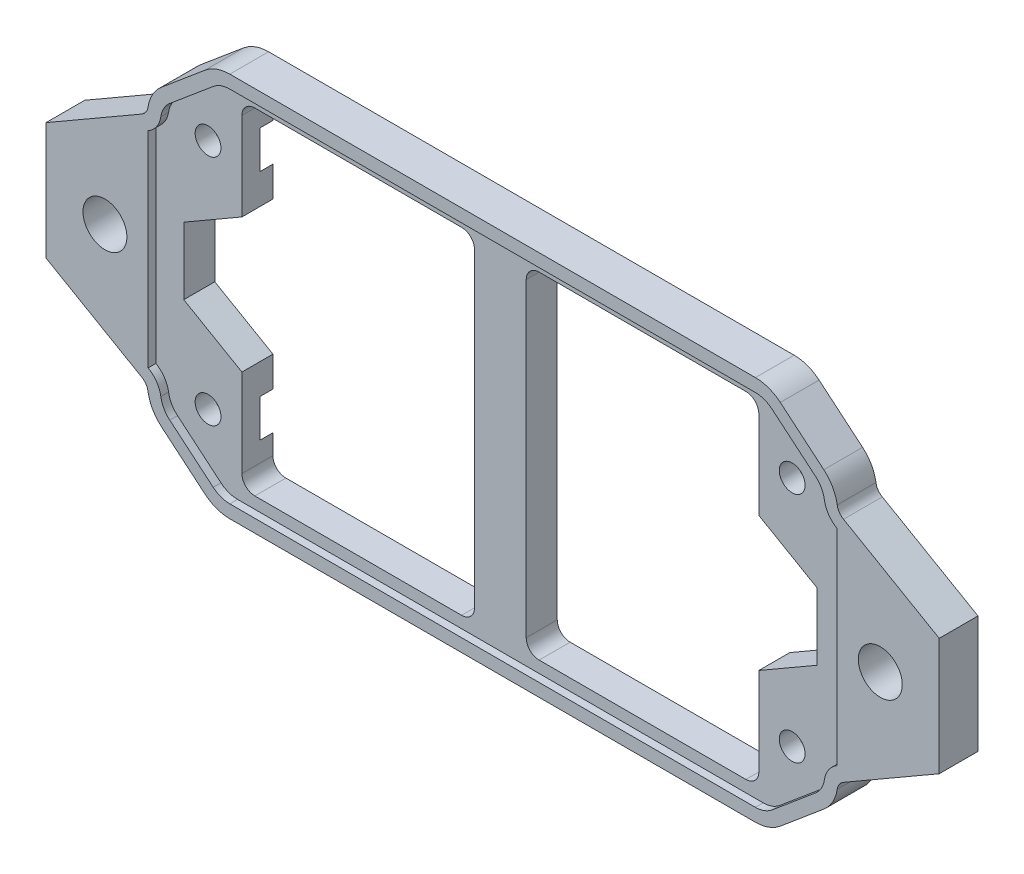
SolidWorks part; units mm, degrees
ref_plane "前视基准面" through (0, 0, 0) normal (0, 0, 1) x (1, 0, 0)
ref_plane "上视基准面" through (0, 0, 0) normal (0, 1, 0) x (1, 0, 0)
ref_plane "右视基准面" through (0, 0, 0) normal (1, 0, 0) x (0, 0, -1)
sketch "草图1" plane through (0, 0, 0) normal (0, 0, 1) x (1, 0, 0)
  line L0 (-6.82, 22.2889) -> (-10.184, 25.1116) construction
  line L1 (-6.4628, 3.3683) -> (-6.4628, 21.5229) construction
  line L2 (-10.184, -0.2205) -> (-6.82, 2.6022) construction
  line L3 (-51.4988, -0.4544) -> (-10.8267, -0.4544) construction
  line L4 (-55.5056, 2.6022) -> (-52.1416, -0.2205) construction
  line L5 (-55.8628, 21.5229) -> (-55.8628, 3.3683) construction
  line L6 (-10.8267, 25.3456) -> (-51.4988, 25.3456) construction
  line L7 (-52.1416, 25.1116) -> (-55.5056, 22.2889) construction
  line L8 (-53.7823, 21.4456) -> (-53.7823, 3.4456) construction
  line L9 (-53.7823, 3.4456) -> (-8.5823, 3.4456) construction
  line L10 (-8.5823, 3.4456) -> (-8.5823, 21.4456) construction
  line L11 (-8.5823, 21.4456) -> (-53.7823, 21.4456) construction
  line L12 (-52.7844, 25.8777) -> (-56.1484, 23.0549)
  line L13 (-56.8628, 21.5229) -> (-56.8628, 3.3683)
  line L14 (-56.1484, 1.8362) -> (-52.7844, -0.9865)
  line L15 (-51.4988, -1.4544) -> (-10.8267, -1.4544)
  line L16 (-9.5412, -0.9865) -> (-6.1772, 1.8362)
  line L17 (-5.4628, 3.3683) -> (-5.4628, 21.5229)
  line L18 (-6.1772, 23.0549) -> (-9.5412, 25.8777)
  line L19 (-10.8267, 26.3456) -> (-51.4988, 26.3456)
  line L20 (-53.4272, 26.6437) -> (-56.7911, 23.821)
  line L28 (-56.7911, 1.0701) -> (-53.4272, -1.7526)
  line L29 (-51.4988, -2.4544) -> (-10.8267, -2.4544)
  line L30 (-8.8984, -1.7526) -> (-5.5344, 1.0701)
  line L32 (-5.5344, 23.821) -> (-8.8984, 26.6437)
  line L33 (-10.8267, 27.3456) -> (-51.4988, 27.3456)
  line L34 (-57.8628, 12.4456) -> (-4.4628, 12.4456) construction
  line L35 (-57.8628, 21.5229) -> (-57.8628, 3.3683) construction
  line L36 (-58.3169, 21.2606) -> (-65.7239, 16.9842)
  line L37 (-65.7239, 16.9842) -> (-65.7239, 7.9069)
  line L38 (-65.7239, 7.9069) -> (-58.3169, 3.6305)
  line L42 (-50.0016, 7.9069) -> (-50.0016, 12.4456) [skipped]
  line L43 (-57.8628, 3.3683) -> (-56.8628, 3.9456) [skipped]
  line L44 (-53.7823, 19.167) -> (-53.9322, 19.2535) [skipped]
  line L45 (-31.1628, 27.3456) -> (-31.1628, -2.4544) construction
  line L46 (3.3984, 7.9069) -> (-4.0086, 3.6305)
  line L47 (3.3984, 16.9842) -> (3.3984, 7.9069)
  line L48 (-4.0086, 21.2606) -> (3.3984, 16.9842)
  line L49 (-4.4628, 3.3683) -> (-4.4628, 21.5229) construction
  arc A0 (-53.7823, 4.4456) -> (-53.7823, 2.4456) centre (-53.7823, 3.4456) ccw
  arc A1 (-53.7823, 2.4456) -> (-53.7823, 4.4456) centre (-53.7823, 3.4456) ccw
  arc A2 (-53.7823, 22.4456) -> (-53.7823, 20.4456) centre (-53.7823, 21.4456) ccw
  arc A3 (-53.7823, 20.4456) -> (-53.7823, 22.4456) centre (-53.7823, 21.4456) ccw
  arc A4 (-8.5823, 4.4456) -> (-8.5823, 2.4456) centre (-8.5823, 3.4456) ccw
  arc A5 (-8.5823, 2.4456) -> (-8.5823, 4.4456) centre (-8.5823, 3.4456) ccw
  arc A6 (-8.5823, 22.4456) -> (-8.5823, 20.4456) centre (-8.5823, 21.4456) ccw
  arc A7 (-8.5823, 20.4456) -> (-8.5823, 22.4456) centre (-8.5823, 21.4456) ccw
  arc A8 (-10.184, 25.1116) -> (-10.8267, 25.3456) centre (-10.8267, 24.3456) ccw construction
  arc A9 (-6.4628, 21.5229) -> (-6.82, 22.2889) centre (-7.4628, 21.5229) ccw construction
  arc A10 (-6.82, 2.6022) -> (-6.4628, 3.3683) centre (-7.4628, 3.3683) ccw construction
  arc A11 (-10.8267, -0.4544) -> (-10.184, -0.2205) centre (-10.8267, 0.5456) ccw construction
  arc A12 (-52.1416, -0.2205) -> (-51.4988, -0.4544) centre (-51.4988, 0.5456) ccw construction
  arc A13 (-55.8628, 3.3683) -> (-55.5056, 2.6022) centre (-54.8628, 3.3683) ccw construction
  arc A14 (-55.5056, 22.2889) -> (-55.8628, 21.5229) centre (-54.8628, 21.5229) ccw construction
  arc A15 (-51.4988, 25.3456) -> (-52.1416, 25.1116) centre (-51.4988, 24.3456) ccw construction
  arc A16 (-56.1484, 23.0549) -> (-56.8628, 21.5229) centre (-54.8628, 21.5229) ccw
  arc A17 (-56.8628, 3.3683) -> (-56.1484, 1.8362) centre (-54.8628, 3.3683) ccw
  arc A18 (-52.7844, -0.9865) -> (-51.4988, -1.4544) centre (-51.4988, 0.5456) ccw
  arc A19 (-10.8267, -1.4544) -> (-9.5412, -0.9865) centre (-10.8267, 0.5456) ccw
  arc A20 (-6.1772, 1.8362) -> (-5.4628, 3.3683) centre (-7.4628, 3.3683) ccw
  arc A21 (-5.4628, 21.5229) -> (-6.1772, 23.0549) centre (-7.4628, 21.5229) ccw
  arc A22 (-9.5412, 25.8777) -> (-10.8267, 26.3456) centre (-10.8267, 24.3456) ccw
  arc A23 (-51.4988, 26.3456) -> (-52.7844, 25.8777) centre (-51.4988, 24.3456) ccw
  arc A24 (-56.7911, 23.821) -> (-57.8284, 21.9757) centre (-54.8628, 21.5229) ccw
  arc A25 (-57.8284, 2.9154) -> (-56.7911, 1.0701) centre (-54.8628, 3.3683) ccw
  arc A26 (-53.4272, -1.7526) -> (-51.4988, -2.4544) centre (-51.4988, 0.5456) ccw
  arc A27 (-10.8267, -2.4544) -> (-8.8984, -1.7526) centre (-10.8267, 0.5456) ccw
  arc A28 (-5.5344, 1.0701) -> (-4.4972, 2.9154) centre (-7.4628, 3.3683) ccw
  arc A29 (-4.4972, 21.9757) -> (-5.5344, 23.821) centre (-7.4628, 21.5229) ccw
  arc A30 (-8.8984, 26.6437) -> (-10.8267, 27.3456) centre (-10.8267, 24.3456) ccw
  arc A31 (-51.4988, 27.3456) -> (-53.4272, 26.6437) centre (-51.4988, 24.3456) ccw
  arc A32 (-57.8628, 3.3683) -> (-56.7911, 1.0701) centre (-54.8628, 3.3683) ccw construction
  arc A33 (-58.3169, 3.6305) -> (-57.8284, 2.9154) centre (-58.8169, 2.7645) cw
  arc A34 (-56.7911, 23.821) -> (-57.8628, 21.5229) centre (-54.8628, 21.5229) ccw construction
  arc A35 (-57.8284, 21.9757) -> (-58.3169, 21.2606) centre (-58.8169, 22.1267) cw
  arc A36 (-4.4972, 21.9757) -> (-4.0086, 21.2606) centre (-3.5086, 22.1267) ccw
  arc A37 (-4.0086, 3.6305) -> (-4.4972, 2.9154) centre (-3.5086, 2.7645) ccw
  arc A38 (-4.4628, 21.5229) -> (-5.5344, 23.821) centre (-7.4628, 21.5229) ccw construction
  arc A39 (-5.5344, 1.0701) -> (-4.4628, 3.3683) centre (-7.4628, 3.3683) ccw construction
  dimension "D3" = 1
  dimension "D2" = 1
  dimension "D1" = 1
extrude "凸台-拉伸2" add sketch "草图1" along normal blind 3 contours A37 L46 L47 L48 A36 A29 L32 A30 L33 A31 L20 A24 A35 L36 L37 L38 A33 A25 L28 A26 L29 A27 L30 A28 A23 L19 A22 L18 A21 L17 A20 L16 A19 L15 A18 L14 A17 L13 A16 L12 | L19 A23 L12 A16 L13 A17 L14 A18 L15 A19 L16 A20 L17 A21 L18 A22 A1 A0 A3 A2 A5 A4 A7 A6
sketch "草图4" plane through (0, 0, 3) normal (0, 0, 1) x (1, 0, 0)
  line L3 (-56.1484, 1.8362) -> (-52.7844, -0.9865)
  line L4 (-51.4988, -1.4544) -> (-10.8267, -1.4544)
  line L5 (-9.5412, -0.9865) -> (-6.1772, 1.8362)
  line L9 (-6.1772, 23.0549) -> (-9.5412, 25.8777)
  line L10 (-10.8267, 26.3456) -> (-51.4988, 26.3456)
  line L11 (-52.7844, 25.8777) -> (-56.1484, 23.0549)
  line L12 (-4.0086, 3.6305) -> (3.3984, 7.9069)
  line L13 (3.3984, 7.9069) -> (3.3984, 16.9842)
  line L14 (3.3984, 16.9842) -> (-4.0086, 21.2606)
  line L15 (-5.5344, 23.821) -> (-8.8984, 26.6437)
  line L16 (-10.8267, 27.3456) -> (-51.4988, 27.3456)
  line L17 (-53.4272, 26.6437) -> (-56.7911, 23.821)
  line L18 (-58.3169, 21.2606) -> (-65.7239, 16.9842)
  line L19 (-65.7239, 16.9842) -> (-65.7239, 7.9069)
  line L20 (-65.7239, 7.9069) -> (-58.3169, 3.6305)
  line L21 (-56.7911, 1.0701) -> (-53.4272, -1.7526)
  line L22 (-51.4988, -2.4544) -> (-10.8267, -2.4544)
  line L23 (-8.8984, -1.7526) -> (-5.5344, 1.0701)
  line L24 (-4.0086, 3.6305) -> (3.3984, 7.9069)
  line L25 (3.3984, 7.9069) -> (3.3984, 16.9842)
  line L26 (3.3984, 16.9842) -> (-4.0086, 21.2606)
  line L27 (-5.5344, 23.821) -> (-8.8984, 26.6437)
  line L28 (-10.8267, 27.3456) -> (-51.4988, 27.3456)
  line L29 (-53.4272, 26.6437) -> (-56.7911, 23.821)
  line L30 (-58.3169, 21.2606) -> (-65.7239, 16.9842)
  line L31 (-65.7239, 16.9842) -> (-65.7239, 7.9069)
  line L32 (-65.7239, 7.9069) -> (-58.3169, 3.6305)
  line L33 (-56.7911, 1.0701) -> (-53.4272, -1.7526)
  line L34 (-51.4988, -2.4544) -> (-10.8267, -2.4544)
  line L35 (-8.8984, -1.7526) -> (-5.5344, 1.0701)
  line L36 (-57.8169, 20.3946) -> (-57.8169, 4.4965)
  line L37 (-4.5086, 20.3946) -> (-4.5086, 4.4965)
  line L38 (-57.8169, 20.3946) -> (-64.7239, 16.4069) construction
  line L39 (-64.7239, 16.4069) -> (-64.7239, 8.4843) construction
  line L40 (-64.7239, 8.4843) -> (-57.8169, 4.4965) construction
  line L41 (2.3984, 8.4843) -> (2.3984, 16.4069) construction
  line L42 (2.3984, 16.4069) -> (-4.5086, 20.3946) construction
  line L43 (-4.5086, 4.4965) -> (2.3984, 8.4843) construction
  arc A0 (-56.8399, 3.0664) -> (-57.8169, 4.4965) centre (-58.8169, 2.7645) ccw
  arc A1 (-56.8399, 3.0664) -> (-56.1484, 1.8362) centre (-54.8628, 3.3683) ccw
  arc A2 (-52.7844, -0.9865) -> (-51.4988, -1.4544) centre (-51.4988, 0.5456) ccw
  arc A3 (-10.8267, -1.4544) -> (-9.5412, -0.9865) centre (-10.8267, 0.5456) ccw
  arc A4 (-6.1772, 1.8362) -> (-5.4857, 3.0664) centre (-7.4628, 3.3683) ccw
  arc A5 (-4.5086, 4.4965) -> (-5.4857, 3.0664) centre (-3.5086, 2.7645) ccw
  arc A6 (-5.4857, 21.8248) -> (-4.5086, 20.3946) centre (-3.5086, 22.1267) ccw
  arc A7 (-5.4857, 21.8248) -> (-6.1772, 23.0549) centre (-7.4628, 21.5229) ccw
  arc A8 (-9.5412, 25.8777) -> (-10.8267, 26.3456) centre (-10.8267, 24.3456) ccw
  arc A9 (-51.4988, 26.3456) -> (-52.7844, 25.8777) centre (-51.4988, 24.3456) ccw
  arc A10 (-56.1484, 23.0549) -> (-56.8399, 21.8248) centre (-54.8628, 21.5229) ccw
  arc A11 (-57.8169, 20.3946) -> (-56.8399, 21.8248) centre (-58.8169, 22.1267) ccw
  arc A12 (-4.0086, 3.6305) -> (-4.4972, 2.9154) centre (-3.5086, 2.7645) ccw
  arc A13 (-4.4972, 21.9757) -> (-4.0086, 21.2606) centre (-3.5086, 22.1267) ccw
  arc A14 (-4.4972, 21.9757) -> (-5.5344, 23.821) centre (-7.4628, 21.5229) ccw
  arc A15 (-8.8984, 26.6437) -> (-10.8267, 27.3456) centre (-10.8267, 24.3456) ccw
  arc A16 (-51.4988, 27.3456) -> (-53.4272, 26.6437) centre (-51.4988, 24.3456) ccw
  arc A17 (-56.7911, 23.821) -> (-57.8284, 21.9757) centre (-54.8628, 21.5229) ccw
  arc A18 (-58.3169, 21.2606) -> (-57.8284, 21.9757) centre (-58.8169, 22.1267) ccw
  arc A19 (-57.8284, 2.9154) -> (-58.3169, 3.6305) centre (-58.8169, 2.7645) ccw
  arc A20 (-57.8284, 2.9154) -> (-56.7911, 1.0701) centre (-54.8628, 3.3683) ccw
  arc A21 (-53.4272, -1.7526) -> (-51.4988, -2.4544) centre (-51.4988, 0.5456) ccw
  arc A22 (-10.8267, -2.4544) -> (-8.8984, -1.7526) centre (-10.8267, 0.5456) ccw
  arc A23 (-5.5344, 1.0701) -> (-4.4972, 2.9154) centre (-7.4628, 3.3683) ccw
  arc A24 (-4.0086, 3.6305) -> (-4.4972, 2.9154) centre (-3.5086, 2.7645) ccw
  arc A25 (-4.4972, 21.9757) -> (-4.0086, 21.2606) centre (-3.5086, 22.1267) ccw
  arc A26 (-4.4972, 21.9757) -> (-5.5344, 23.821) centre (-7.4628, 21.5229) ccw
  arc A27 (-8.8984, 26.6437) -> (-10.8267, 27.3456) centre (-10.8267, 24.3456) ccw
  arc A28 (-51.4988, 27.3456) -> (-53.4272, 26.6437) centre (-51.4988, 24.3456) ccw
  arc A29 (-56.7911, 23.821) -> (-57.8284, 21.9757) centre (-54.8628, 21.5229) ccw
  arc A30 (-58.3169, 21.2606) -> (-57.8284, 21.9757) centre (-58.8169, 22.1267) ccw
  arc A31 (-57.8284, 2.9154) -> (-58.3169, 3.6305) centre (-58.8169, 2.7645) ccw
  arc A32 (-57.8284, 2.9154) -> (-56.7911, 1.0701) centre (-54.8628, 3.3683) ccw
  arc A33 (-53.4272, -1.7526) -> (-51.4988, -2.4544) centre (-51.4988, 0.5456) ccw
  arc A34 (-10.8267, -2.4544) -> (-8.8984, -1.7526) centre (-10.8267, 0.5456) ccw
  arc A35 (-5.5344, 1.0701) -> (-4.4972, 2.9154) centre (-7.4628, 3.3683) ccw
  dimension "D1" = 0
  dimension "D2" = 1
extrude "切除-拉伸1" cut sketch "草图4" against normal blind 0.6 contours A5 A4 L5 A3 L4 A2 L3 A1 A0 L36 A11 A10 L11 A9 L10 A8 L9 A7 A6 L37
sketch "草图6" plane through (0, 0, 2.4) normal (0, 0, 1) x (1, 0, 0)
  line L0 (-65.7239, 12.4456) -> (3.3984, 12.4456) construction
  line L3 (-65.7239, 16.9842) -> (-65.7239, 7.9069) construction
  line L4 (3.3984, 16.9842) -> (3.3984, 7.9069) construction
  line L5 (-31.1628, -0.5544) -> (-31.1628, 27.3456) construction
  line L7 (-10.8267, 27.3456) -> (-51.4988, 27.3456) construction
  line L8 (-29.1628, 25.4456) -> (-11.1628, 25.4456)
  line L9 (-51.1628, -0.5544) -> (-33.1628, -0.5544)
  line L10 (-51.1628, -0.5544) -> (-51.1628, 25.4456)
  line L11 (-51.1628, 25.4456) -> (-33.1628, 25.4456)
  line L12 (-11.1628, -0.5544) -> (-11.1628, 25.4456)
  line L13 (-51.1628, -0.5544) -> (-11.1628, 25.4456) construction
  line L14 (-51.1628, 25.4456) -> (-11.1628, -0.5544) construction
  line L16 (-29.1628, -0.5544) -> (-29.1628, 25.4456)
  line L18 (-33.1628, -0.5544) -> (-33.1628, 25.4456)
  line L19 (-31.0525, 12.3739) -> (-31.0602, 12.4456) construction
  line L20 (-29.1628, -0.5544) -> (-11.1628, -0.5544)
  line L21 (-31.0602, 12.4456) -> (-31.1628, 11.5603) construction
  point P12 (-31.1628, 12.4456)
  point P17 (-31.1628, 13.3956)
  dimension "D1" = 40
  dimension "D2" = 26
extrude "切除-拉伸4" cut sketch "草图6" against normal through all
fillet "圆角1" radius 1 4 edges at (-33.1628, -0.5544, 1.2) (-29.1628, -0.5544, 1.2) (-29.1628, 25.4456, 1.2) (-33.1628, 25.4456, 1.2)
sketch "草图10" plane through (0, 0, 2.4) normal (0, 0, 1) x (1, 0, 0)
  line L0 (-65.7239, 12.4456) -> (3.3984, 12.4456) construction
  line L1 (-65.7239, 16.9842) -> (-65.7239, 7.9069) construction
  line L2 (3.3984, 16.9842) -> (3.3984, 7.9069) construction
  line L3 (-11.1628, 7.2494) -> (-11.1628, 17.6417)
  line L4 (-51.1628, 7.2494) -> (-51.1628, 17.6417)
  line L6 (-11.1628, 7.2494) -> (-6.6628, 9.8475)
  line L7 (-6.6628, 9.8475) -> (-6.6628, 15.0436)
  line L8 (-6.6628, 15.0436) -> (-11.1628, 17.6417)
  line L15 (-51.1628, 17.6417) -> (-55.6628, 15.0436)
  line L16 (-55.6628, 15.0436) -> (-55.6628, 9.8475)
  line L17 (-55.6628, 9.8475) -> (-51.1628, 7.2494)
  line L18 (-46.6628, 9.8475) -> (-46.6628, 12.4456) [skipped]
  line L19 (-15.6628, 12.4456) -> (-15.6628, 9.8475) [skipped]
  line L20 (-15.6628, 9.8475) -> (-11.1628, 7.2494) [skipped]
  line L21 (-13.4128, 16.3427) -> (-15.6628, 15.0436) [skipped]
  line L22 (-48.9128, 16.3427) -> (-51.1628, 17.6417) [skipped]
  line L23 (-51.1628, 7.2494) -> (-48.9128, 8.5484) [skipped]
  arc A0 (-11.1628, 7.9456) -> (-11.1628, 16.9456) centre (-11.1628, 12.4456) ccw construction
  arc A1 (-51.1628, 16.9456) -> (-51.1628, 7.9456) centre (-51.1628, 12.4456) ccw construction
  dimension "D1" = 9
  dimension "D2" = 9
extrude "切除-拉伸6" cut sketch "草图10" against normal through all
fillet "圆角2" radius 1 4 edges at (-51.1628, -0.5544, 1.2) (-11.1628, -0.5544, 1.2) (-11.1628, 25.4456, 1.2) (-51.1628, 25.4456, 1.2)
sketch "草图11" plane through (0, 0, 0) normal (0, 0, -1) x (-1, 0, 0)
  line L1 (9.7659, 19.3956) -> (10.9494, 21.4456)
  line L2 (10.9494, 21.4456) -> (9.7659, 23.4956)
  line L3 (9.7659, 23.4956) -> (7.3987, 23.4956)
  line L4 (7.3987, 23.4956) -> (6.2151, 21.4456)
  line L5 (6.2151, 21.4456) -> (7.3987, 19.3956)
  line L6 (7.3987, 19.3956) -> (9.7659, 19.3956)
  line L7 (9.7659, 1.3956) -> (10.9494, 3.4456)
  line L8 (10.9494, 3.4456) -> (9.7659, 5.4956)
  line L9 (9.7659, 5.4956) -> (7.3987, 5.4956)
  line L10 (7.3987, 5.4956) -> (6.2151, 3.4456)
  line L11 (6.2151, 3.4456) -> (7.3987, 1.3956)
  line L12 (7.3987, 1.3956) -> (9.7659, 1.3956)
  line L13 (54.9659, 1.3956) -> (56.1494, 3.4456)
  line L14 (56.1494, 3.4456) -> (54.9659, 5.4956)
  line L15 (54.9659, 5.4956) -> (52.5987, 5.4956)
  line L16 (52.5987, 5.4956) -> (51.4151, 3.4456)
  line L17 (51.4151, 3.4456) -> (52.5987, 1.3956)
  line L18 (52.5987, 1.3956) -> (54.9659, 1.3956)
  line L19 (54.9659, 19.3956) -> (56.1494, 21.4456)
  line L20 (56.1494, 21.4456) -> (54.9659, 23.4956)
  line L21 (54.9659, 23.4956) -> (52.5987, 23.4956)
  line L22 (52.5987, 23.4956) -> (51.4151, 21.4456)
  line L23 (51.4151, 21.4456) -> (52.5987, 19.3956)
  line L24 (52.5987, 19.3956) -> (54.9659, 19.3956)
  circle A0 centre (8.5823, 21.4456) radius 2.05 construction
  circle A1 centre (8.5823, 3.4456) radius 2.05 construction
  circle A2 centre (53.7823, 3.4456) radius 2.05 construction
  circle A3 centre (53.7823, 21.4456) radius 2.05 construction
  dimension "D1" = 4.1
  dimension "D2" = 4.1
  dimension "D3" = 4.1
  dimension "D4" = 4.1
extrude "切除-拉伸7" [suppressed] cut sketch "草图11" against normal blind 1.4
sketch "草图12" [suppressed] plane through (0, 0, 0) normal (0, 0, -1) x (-1, 0, 0)
  line L0 (6.2151, 21.4456) -> (7.3987, 19.3956)
  line L1 (6.2151, 21.4456) -> (5.9553, 21.2956)
  line L2 (7.3987, 19.3956) -> (7.1389, 19.2456)
  line L3 (5.9553, 21.2956) -> (7.1389, 19.2456)
  line L4 (7.3987, 5.4956) -> (6.2151, 3.4456)
  line L5 (7.3987, 5.4956) -> (7.1389, 5.6456)
  line L6 (6.2151, 3.4456) -> (5.9553, 3.5956)
  line L7 (7.1389, 5.6456) -> (5.9553, 3.5956)
  line L8 (54.9659, 5.4956) -> (56.1494, 3.4456)
  line L9 (54.9659, 5.4956) -> (55.2257, 5.6456)
  line L10 (56.1494, 3.4456) -> (56.4092, 3.5956)
  line L11 (55.2257, 5.6456) -> (56.4092, 3.5956)
  line L12 (56.1494, 3.4456) -> (54.9659, 5.4956) construction
  line L13 (56.1494, 3.4456) -> (54.9659, 5.4956) construction
  line L14 (54.9659, 19.3956) -> (56.1494, 21.4456)
  line L15 (54.9659, 19.3956) -> (55.2257, 19.2456)
  line L16 (56.1494, 21.4456) -> (56.4092, 21.2956)
  line L17 (55.2257, 19.2456) -> (56.4092, 21.2956)
  dimension "D1" = 0.3
  dimension "D2" = 0.3
  dimension "D3" = 0.3
  dimension "D4" = 0.3
extrude "切除-拉伸8" [suppressed] cut sketch "草图12" against normal blind 1.4
sketch "草图13" plane through (0, 0, 3) normal (0, 0, 1) x (1, 0, 0)
  line L0 (-58.3169, 21.2606) -> (-58.3169, 3.6305)
  line L1 (-58.3169, 3.6305) -> (-65.7239, 7.9069)
  line L2 (-65.7239, 7.9069) -> (-65.7239, 16.9842)
  line L3 (-65.7239, 16.9842) -> (-58.3169, 21.2606)
  line L4 (-4.0086, 21.2606) -> (3.3984, 16.9842)
  line L5 (3.3984, 16.9842) -> (3.3984, 7.9069)
  line L6 (3.3984, 7.9069) -> (-4.0086, 3.6305)
  line L7 (-4.0086, 3.6305) -> (-4.0086, 21.2606)
extrude "切除-拉伸9" [suppressed] cut sketch "草图13" against normal through all
sketch "草图14" [suppressed] plane through (0, 0, 3) normal (0, 0, 1) x (1, 0, 0)
  line L0 (-51.4988, -1.4544) -> (-10.8267, -1.4544) construction
  line L1 (-31.1628, 27.3456) -> (-31.1628, -13.7023) construction
  line L2 (-4.0086, 12.4456) -> (-58.3169, 12.4456) construction
  line L3 (-10.8267, 27.3456) -> (-51.4988, 27.3456) construction
  line L5 (-38.1628, -1.4544) -> (-35.1628, -8.441)
  line L6 (-35.1628, -8.441) -> (-27.1628, -8.441)
  line L7 (-27.1628, -8.441) -> (-24.1628, -1.4544)
  line L16 (-38.1628, 26.3456) -> (-35.1628, 33.3321)
  line L17 (-38.1628, -1.4544) -> (-24.1628, -1.4544)
  line L19 (-4.0086, 21.2606) -> (-4.0086, 3.6305) construction
  line L20 (-58.3169, 3.6305) -> (-58.3169, 21.2606) construction
  line L21 (-35.1628, 33.3321) -> (-27.1628, 33.3321)
  line L22 (-27.1628, 33.3321) -> (-24.1628, 26.3456)
  line L23 (-38.1628, 26.3456) -> (-24.1628, 26.3456)
  dimension "D1" = 8
  dimension "D2" = 14
  dimension "D3" = 6.9865
extrude "凸台-拉伸3" [suppressed] add sketch "草图14" against normal blind 3 separate body
combine bodies "组合1" [suppressed] operation type add bodies to combine 117 119 116
sketch "草图15" [suppressed] plane through (0, 0, 3) normal (0, 0, 1) x (1, 0, 0)
  line L0 (-31.1628, 33.3321) -> (-31.1628, -8.441) construction
  line L1 (-27.1628, 33.3321) -> (-35.1628, 33.3321) construction
  line L2 (-35.1628, -8.441) -> (-27.1628, -8.441) construction
  line L3 (-57.8169, 12.4456) -> (8.4653, 12.4456) construction
  line L4 (-57.8169, 20.3946) -> (-57.8169, 4.4965) construction
  circle A0 centre (-31.1628, 28.4456) radius 1.6
  circle A1 centre (-31.1628, -3.5544) radius 1.6
  dimension "D1" = 3.2
  dimension "D2" = 16
extrude "切除-拉伸12" [suppressed] cut sketch "草图15" against normal through all
fillet "圆角3" [suppressed] radius 10
sketch "草图16" [suppressed] plane through (0, 0, 3) normal (0, 0, 1) x (1, 0, 0)
  line L0 (-4.0086, 12.4456) -> (-58.3169, 12.4456) construction
  line L1 (-4.0086, 21.2606) -> (-4.0086, 3.6305) construction
  line L2 (-58.3169, 3.6305) -> (-58.3169, 21.2606) construction
  line L3 (-31.1628, 12.4456) -> (-31.1628, 17.9456) construction
  line L4 (-29.1628, 24.4456) -> (-29.1628, 0.4456) construction
  line L5 (-58.3169, 17.9456) -> (-33.1628, 17.9456)
  line L6 (-58.3169, 17.9456) -> (-58.3169, 6.9456)
  line L7 (-58.3169, 6.9456) -> (-33.1628, 6.9456)
  line L8 (-4.0086, 17.9456) -> (-4.0086, 6.9456)
  line L9 (-58.3169, 17.9456) -> (-4.0086, 6.9456) construction
  line L10 (-58.3169, 6.9456) -> (-4.0086, 17.9456) construction
  line L11 (-33.1628, 0.4456) -> (-33.1628, 24.4456) construction
  line L12 (-29.1628, 17.9456) -> (-29.1628, 6.9456)
  line L13 (-33.1628, 6.9456) -> (-33.1628, 17.9456)
  line L14 (-29.1628, 6.9456) -> (-4.0086, 6.9456)
  line L15 (-29.1628, 17.9456) -> (-4.0086, 17.9456)
  dimension "D1" = 11
extrude "切除-拉伸14" [suppressed] cut sketch "草图16" against normal through all
sketch "草图17" [suppressed] plane through (0, 0, 2.4) normal (0, 0, 1) x (1, 0, 0)
  line L0 (-33.1628, 12.4456) -> (-2.1778, 12.4456) construction
  line L1 (-33.1628, 0.4456) -> (-33.1628, 24.4456) construction
  line L2 (-31.1628, -1.4544) -> (-31.1628, 23.762) construction
  line L3 (-10.8267, -1.4544) -> (-51.4988, -1.4544) construction
  line L5 (-11.1628, 4.8543) -> (-11.1628, 6.9456)
  line L6 (-24.1628, 13.9733) -> (-11.1628, 17.9456)
  line L7 (-29.1628, 24.4456) -> (-29.1628, 0.4456) construction
  line L8 (-24.1628, 10.9178) -> (-11.1628, 6.9456)
  line L9 (-29.1628, 10.3543) -> (-11.1628, 4.8543)
  line L10 (-11.1628, 0.4456) -> (-11.1628, 6.9456) construction
  line L11 (-11.1628, 20.0368) -> (-11.1628, 17.9456)
  line L12 (-29.1628, 14.5368) -> (-11.1628, 20.0368)
  line L22 (-24.1628, 13.9733) -> (-24.1628, 10.9178)
  line L23 (-29.1628, 10.3543) -> (-29.1628, 14.5368)
  line L24 (-11.1628, 6.9456) -> (-4.5086, 6.9456) construction
  line L25 (-33.1628, 10.3543) -> (-51.1628, 4.8543)
  line L26 (-51.1628, 4.8543) -> (-51.1628, 6.9456)
  line L27 (-38.1628, 10.9178) -> (-51.1628, 6.9456)
  line L28 (-38.1628, 13.9733) -> (-38.1628, 10.9178)
  line L29 (-38.1628, 13.9733) -> (-51.1628, 17.9456)
  line L30 (-51.1628, 20.0368) -> (-51.1628, 17.9456)
  line L31 (-33.1628, 14.5368) -> (-51.1628, 20.0368)
  line L32 (-33.1628, 10.3543) -> (-33.1628, 14.5368)
  dimension "D1" = 2
  dimension "D2" = 5
  dimension "D3" = 163.009
extrude "凸台-拉伸5" [suppressed] add sketch "草图17" against normal blind 2.4
fillet "圆角4" [suppressed] radius 1
sketch "草图18" [suppressed] plane through (0, 0, 3) normal (0, 0, 1) x (1, 0, 0)
  line L0 (-24.1628, 12.4456) -> (-38.1628, 12.4456) construction
  line L1 (-24.1628, 10.9178) -> (-24.1628, 13.9733) construction
  line L2 (-38.1628, 13.9733) -> (-38.1628, 10.9178) construction
  line L3 (-31.1628, 26.3456) -> (-31.1628, -1.4544) construction
  line L4 (-51.4988, 26.3456) -> (-10.8267, 26.3456) construction
  line L5 (-51.4988, -1.4544) -> (-10.8267, -1.4544) construction
  line L6 (-58.3169, 6.9456) -> (-57.8169, 6.9456) construction
  line L11 (-58.3169, 17.9456) -> (-57.8169, 17.9456)
  line L12 (-58.3169, 21.2606) -> (-58.3169, 17.9456)
  line L13 (-57.8169, 6.9456) -> (-51.3121, 6.9456) construction
  line L14 (-58.3169, 3.6305) -> (-58.3169, 6.9456) construction
  line L15 (-4.0086, 21.2606) -> (-4.0086, 17.9456)
  line L17 (-5.5344, 23.821) -> (-5.6628, 23.9287)
  line L18 (-5.6628, 17.9456) -> (-5.6628, 23.9287)
  line L21 (-4.5086, 17.9456) -> (-5.6628, 17.9456)
  line L24 (-58.3169, 6.9456) -> (-57.8169, 6.9456)
  line L25 (-57.8169, 6.9456) -> (-56.6628, 6.9456)
  line L26 (-58.3169, 3.6305) -> (-58.3169, 6.9456)
  line L27 (-56.7911, 23.821) -> (-56.6628, 23.9287)
  line L29 (-56.6628, 17.9456) -> (-56.6628, 23.9287)
  line L30 (-57.8169, 17.9456) -> (-56.6628, 17.9456)
  line L33 (-4.0086, 17.9456) -> (-4.5086, 17.9456)
  line L36 (-56.6628, 6.9456) -> (-56.6628, 0.9624)
  line L37 (-56.7911, 1.0701) -> (-53.4272, -1.7526) construction
  line L38 (-56.7911, 1.0701) -> (-56.6628, 0.9624)
  line L39 (-4.0086, 6.9456) -> (-4.5086, 6.9456)
  line L40 (-4.0086, 3.6305) -> (-4.0086, 6.9456)
  line L41 (-5.5344, 1.0701) -> (-5.6628, 0.9624)
  line L42 (-5.6628, 6.9456) -> (-5.6628, 0.9624)
  line L43 (-4.5086, 6.9456) -> (-5.6628, 6.9456)
  arc A0 (-4.4972, 21.9757) -> (-4.0086, 21.2606) centre (-3.5086, 22.1267) ccw
  arc A1 (-57.8284, 2.9154) -> (-56.7911, 1.0701) centre (-54.8628, 3.3683) ccw construction
  arc A2 (-57.8284, 2.9154) -> (-58.3169, 3.6305) centre (-58.8169, 2.7645) ccw construction
  arc A3 (-4.4972, 21.9757) -> (-5.5344, 23.821) centre (-7.4628, 21.5229) ccw
  arc A5 (-4.4972, 2.9154) -> (-4.0086, 3.6305) centre (-3.5086, 2.7645) cw
  arc A9 (-57.8284, 2.9154) -> (-56.7911, 1.0701) centre (-54.8628, 3.3683) ccw
  arc A10 (-57.8284, 2.9154) -> (-58.3169, 3.6305) centre (-58.8169, 2.7645) ccw
  arc A11 (-57.8284, 21.9757) -> (-58.3169, 21.2606) centre (-58.8169, 22.1267) cw
  arc A13 (-57.8284, 21.9757) -> (-56.7911, 23.821) centre (-54.8628, 21.5229) cw
  arc A14 (-4.4972, 2.9154) -> (-5.5344, 1.0701) centre (-7.4628, 3.3683) cw
  point P12 (-31.1628, 12.4456)
  dimension "D1" = 25.5
extrude "切除-拉伸15" [suppressed] cut sketch "草图18" against normal through all
fillet "圆角5" [suppressed] radius 1
sketch "草图19" [suppressed] plane through (0, 0, 0) normal (0, 0, -1) x (-1, 0, 0)
  line L0 (10.9494, 3.4456) -> (9.7659, 5.4956) construction
  line L1 (9.7659, 1.3956) -> (10.9494, 3.4456) construction
  line L2 (7.3987, 1.3956) -> (9.7659, 1.3956) construction
  line L3 (10.9494, 21.4456) -> (9.7659, 23.4956) construction
  line L4 (51.1628, 20.0368) -> (51.1628, 24.4456)
  line L5 (33.1628, 14.5368) -> (51.1628, 20.0368)
  line L6 (33.1628, 24.4456) -> (33.1628, 14.5368)
  line L7 (50.1628, 25.4456) -> (34.1628, 25.4456)
  line L8 (7.1389, 5.6456) -> (5.9553, 3.5956)
  line L9 (7.3987, 5.4956) -> (7.1389, 5.6456)
  line L10 (9.7659, 5.4956) -> (7.3987, 5.4956)
  line L11 (10.9494, 3.4456) -> (9.7659, 5.4956)
  line L12 (9.7659, 1.3956) -> (10.9494, 3.4456)
  line L13 (7.3987, 1.3956) -> (9.7659, 1.3956)
  line L14 (6.2151, 3.4456) -> (7.3987, 1.3956)
  line L15 (5.9553, 3.5956) -> (6.2151, 3.4456)
  line L16 (7.1389, 5.6456) -> (5.9553, 3.5956)
  line L17 (7.3987, 5.4956) -> (7.1389, 5.6456)
  line L18 (9.7659, 5.4956) -> (7.3987, 5.4956)
  line L19 (10.9494, 3.4456) -> (9.7659, 5.4956)
  line L20 (9.7659, 1.3956) -> (10.9494, 3.4456)
  line L21 (7.3987, 1.3956) -> (9.7659, 1.3956)
  line L22 (6.2151, 3.4456) -> (7.3987, 1.3956)
  line L23 (5.9553, 3.5956) -> (6.2151, 3.4456)
  line L24 (8.8984, 26.6437) -> (6.02, 24.2284)
  line L25 (5.6628, 23.4624) -> (5.6628, 17.9456)
  line L26 (5.6628, 17.9456) -> (11.0134, 17.9456)
  line L27 (11.3056, 17.9019) -> (24.1628, 13.9733)
  line L28 (24.1628, 13.9733) -> (24.1628, 10.9178)
  line L29 (24.1628, 10.9178) -> (11.3056, 6.9892)
  line L30 (11.0134, 6.9456) -> (5.6628, 6.9456)
  line L31 (5.6628, 6.9456) -> (5.6628, 1.4287)
  line L32 (6.02, 0.6627) -> (8.8984, -1.7526)
  line L33 (10.8267, -2.4544) -> (18.0035, -2.4544)
  line L34 (27.1628, -8.441) -> (35.1628, -8.441)
  line L35 (44.322, -2.4544) -> (51.4988, -2.4544)
  line L36 (53.4272, -1.7526) -> (56.3056, 0.6627)
  line L37 (56.6628, 1.4287) -> (56.6628, 6.9456)
  line L38 (56.6628, 6.9456) -> (51.3121, 6.9456)
  line L39 (51.0199, 6.9892) -> (38.1628, 10.9178)
  line L40 (38.1628, 10.9178) -> (38.1628, 13.9733)
  line L41 (38.1628, 13.9733) -> (51.0199, 17.9019)
  line L42 (51.3121, 17.9456) -> (56.6628, 17.9456)
  line L43 (56.6628, 17.9456) -> (56.6628, 23.4624)
  line L44 (56.3056, 24.2284) -> (53.4272, 26.6437)
  line L45 (51.4988, 27.3456) -> (44.322, 27.3456)
  line L46 (35.1628, 33.3321) -> (27.1628, 33.3321)
  line L47 (18.0035, 27.3456) -> (10.8267, 27.3456)
  line L48 (8.8984, 26.6437) -> (6.02, 24.2284)
  line L49 (5.6628, 23.4624) -> (5.6628, 17.9456)
  line L50 (5.6628, 17.9456) -> (11.0134, 17.9456)
  line L51 (11.3056, 17.9019) -> (24.1628, 13.9733)
  line L52 (24.1628, 13.9733) -> (24.1628, 10.9178)
  line L53 (24.1628, 10.9178) -> (11.3056, 6.9892)
  line L54 (11.0134, 6.9456) -> (5.6628, 6.9456)
  line L55 (5.6628, 6.9456) -> (5.6628, 1.4287)
  line L56 (6.02, 0.6627) -> (8.8984, -1.7526)
  line L57 (10.8267, -2.4544) -> (18.0035, -2.4544)
  line L58 (27.1628, -8.441) -> (35.1628, -8.441)
  line L59 (44.322, -2.4544) -> (51.4988, -2.4544)
  line L60 (53.4272, -1.7526) -> (56.3056, 0.6627)
  line L61 (56.6628, 1.4287) -> (56.6628, 6.9456)
  line L62 (56.6628, 6.9456) -> (51.3121, 6.9456)
  line L63 (51.0199, 6.9892) -> (38.1628, 10.9178)
  line L64 (38.1628, 10.9178) -> (38.1628, 13.9733)
  line L65 (38.1628, 13.9733) -> (51.0199, 17.9019)
  line L66 (51.3121, 17.9456) -> (56.6628, 17.9456)
  line L67 (56.6628, 17.9456) -> (56.6628, 23.4624)
  line L68 (56.3056, 24.2284) -> (53.4272, 26.6437)
  line L69 (51.4988, 27.3456) -> (44.322, 27.3456)
  line L70 (35.1628, 33.3321) -> (27.1628, 33.3321)
  line L71 (18.0035, 27.3456) -> (10.8267, 27.3456)
  line L72 (5.9553, 21.2956) -> (7.1389, 19.2456)
  line L73 (6.2151, 21.4456) -> (5.9553, 21.2956)
  line L74 (7.3987, 23.4956) -> (6.2151, 21.4456)
  line L75 (9.7659, 23.4956) -> (7.3987, 23.4956)
  line L76 (10.9494, 21.4456) -> (9.7659, 23.4956)
  line L77 (9.7659, 19.3956) -> (10.9494, 21.4456)
  line L78 (7.3987, 19.3956) -> (9.7659, 19.3956)
  line L79 (7.1389, 19.2456) -> (7.3987, 19.3956)
  line L80 (5.9553, 21.2956) -> (7.1389, 19.2456)
  line L81 (6.2151, 21.4456) -> (5.9553, 21.2956)
  line L82 (7.3987, 23.4956) -> (6.2151, 21.4456)
  line L83 (9.7659, 23.4956) -> (7.3987, 23.4956)
  line L84 (10.9494, 21.4456) -> (9.7659, 23.4956)
  line L85 (9.7659, 19.3956) -> (10.9494, 21.4456)
  line L86 (7.3987, 19.3956) -> (9.7659, 19.3956)
  line L87 (7.1389, 19.2456) -> (7.3987, 19.3956)
  line L88 (55.2257, 19.2456) -> (56.4092, 21.2956)
  line L89 (54.9659, 19.3956) -> (55.2257, 19.2456)
  line L90 (52.5987, 19.3956) -> (54.9659, 19.3956)
  line L91 (51.4151, 21.4456) -> (52.5987, 19.3956)
  line L92 (52.5987, 23.4956) -> (51.4151, 21.4456)
  line L93 (54.9659, 23.4956) -> (52.5987, 23.4956)
  line L94 (56.1494, 21.4456) -> (54.9659, 23.4956)
  line L95 (56.4092, 21.2956) -> (56.1494, 21.4456)
  line L96 (55.2257, 19.2456) -> (56.4092, 21.2956)
  line L97 (54.9659, 19.3956) -> (55.2257, 19.2456)
  line L98 (52.5987, 19.3956) -> (54.9659, 19.3956)
  line L99 (51.4151, 21.4456) -> (52.5987, 19.3956)
  line L100 (52.5987, 23.4956) -> (51.4151, 21.4456)
  line L101 (54.9659, 23.4956) -> (52.5987, 23.4956)
  line L102 (56.1494, 21.4456) -> (54.9659, 23.4956)
  line L103 (56.4092, 21.2956) -> (56.1494, 21.4456)
  line L104 (51.1628, 20.0368) -> (51.1628, 24.4456)
  line L105 (33.1628, 14.5368) -> (51.1628, 20.0368)
  line L106 (33.1628, 24.4456) -> (33.1628, 14.5368)
  line L107 (50.1628, 25.4456) -> (34.1628, 25.4456)
  line L108 (11.1628, 20.0368) -> (29.1628, 14.5368)
  line L109 (11.1628, 24.4456) -> (11.1628, 20.0368)
  line L110 (28.1628, 25.4456) -> (12.1628, 25.4456)
  line L111 (29.1628, 14.5368) -> (29.1628, 24.4456)
  line L112 (11.1628, 20.0368) -> (29.1628, 14.5368)
  line L113 (11.1628, 24.4456) -> (11.1628, 20.0368)
  line L114 (28.1628, 25.4456) -> (12.1628, 25.4456)
  line L115 (29.1628, 14.5368) -> (29.1628, 24.4456)
  line L116 (11.1628, 4.8543) -> (11.1628, 0.4456)
  line L117 (29.1628, 10.3543) -> (11.1628, 4.8543)
  line L118 (29.1628, 0.4456) -> (29.1628, 10.3543)
  line L119 (12.1628, -0.5544) -> (28.1628, -0.5544)
  line L120 (11.1628, 4.8543) -> (11.1628, 0.4456)
  line L121 (29.1628, 10.3543) -> (11.1628, 4.8543)
  line L122 (29.1628, 0.4456) -> (29.1628, 10.3543)
  line L123 (12.1628, -0.5544) -> (28.1628, -0.5544)
  line L124 (51.1628, 4.8543) -> (33.1628, 10.3543)
  line L125 (51.1628, 0.4456) -> (51.1628, 4.8543)
  line L126 (34.1628, -0.5544) -> (50.1628, -0.5544)
  line L127 (33.1628, 10.3543) -> (33.1628, 0.4456)
  line L128 (51.1628, 4.8543) -> (33.1628, 10.3543)
  line L129 (51.1628, 0.4456) -> (51.1628, 4.8543)
  line L130 (34.1628, -0.5544) -> (50.1628, -0.5544)
  line L131 (33.1628, 10.3543) -> (33.1628, 0.4456)
  line L132 (52.5987, 23.4956) -> (51.4151, 21.4456) construction
  line L133 (10.9494, 3.4456) -> (9.7659, 5.4956)
  line L134 (9.7659, 1.3956) -> (10.9494, 3.4456)
  line L135 (7.3987, 1.3956) -> (9.7659, 1.3956)
  line L136 (54.9659, 5.4956) -> (52.5987, 5.4956)
  line L137 (55.2257, 5.6456) -> (54.9659, 5.4956)
  line L138 (56.4092, 3.5956) -> (55.2257, 5.6456)
  line L139 (56.1494, 3.4456) -> (56.4092, 3.5956)
  line L140 (54.9659, 1.3956) -> (56.1494, 3.4456)
  line L141 (52.5987, 1.3956) -> (54.9659, 1.3956)
  line L142 (51.4151, 3.4456) -> (52.5987, 1.3956)
  line L143 (52.5987, 5.4956) -> (51.4151, 3.4456)
  line L144 (54.9659, 5.4956) -> (52.5987, 5.4956)
  line L145 (55.2257, 5.6456) -> (54.9659, 5.4956)
  line L146 (56.4092, 3.5956) -> (55.2257, 5.6456)
  line L147 (56.1494, 3.4456) -> (56.4092, 3.5956)
  line L148 (54.9659, 1.3956) -> (56.1494, 3.4456)
  line L149 (52.5987, 1.3956) -> (54.9659, 1.3956)
  line L150 (51.4151, 3.4456) -> (52.5987, 1.3956)
  line L151 (52.5987, 5.4956) -> (51.4151, 3.4456)
  line L152 (10.9494, 21.4456) -> (9.7659, 23.4956)
  line L153 (52.5987, 23.4956) -> (51.4151, 21.4456)
  circle A1 centre (31.1628, 28.4456) radius 1.6
  circle A2 centre (31.1628, 28.4456) radius 1.6
  circle A3 centre (31.1628, -3.5544) radius 1.6
  arc A4 (34.1628, 25.4456) -> (33.1628, 24.4456) centre (34.1628, 24.4456) ccw
  arc A5 (51.1628, 24.4456) -> (50.1628, 25.4456) centre (50.1628, 24.4456) ccw
  arc A6 (34.1628, 25.4456) -> (33.1628, 24.4456) centre (34.1628, 24.4456) ccw
  arc A7 (51.1628, 24.4456) -> (50.1628, 25.4456) centre (50.1628, 24.4456) ccw
  arc A8 (12.1628, 25.4456) -> (11.1628, 24.4456) centre (12.1628, 24.4456) ccw
  arc A9 (29.1628, 24.4456) -> (28.1628, 25.4456) centre (28.1628, 24.4456) ccw
  arc A10 (12.1628, 25.4456) -> (11.1628, 24.4456) centre (12.1628, 24.4456) ccw
  arc A11 (29.1628, 24.4456) -> (28.1628, 25.4456) centre (28.1628, 24.4456) ccw
  circle A12 centre (31.1628, -3.5544) radius 1.6
  circle A13 centre (53.7823, 21.4456) radius 1
  arc A14 (28.1628, -0.5544) -> (29.1628, 0.4456) centre (28.1628, 0.4456) ccw
  arc A15 (11.1628, 0.4456) -> (12.1628, -0.5544) centre (12.1628, 0.4456) ccw
  arc A16 (6.02, 24.2284) -> (5.6628, 23.4624) centre (6.6628, 23.4624) ccw
  arc A17 (11.3056, 17.9019) -> (11.0134, 17.9456) centre (11.0134, 16.9456) ccw
  arc A18 (11.0134, 6.9456) -> (11.3056, 6.9892) centre (11.0134, 7.9456) ccw
  arc A19 (5.6628, 1.4287) -> (6.02, 0.6627) centre (6.6628, 1.4287) ccw
  arc A20 (8.8984, -1.7526) -> (10.8267, -2.4544) centre (10.8267, 0.5456) ccw
  arc A21 (27.1628, -8.441) -> (18.0035, -2.4544) centre (18.0035, -12.4544) ccw
  arc A22 (44.322, -2.4544) -> (35.1628, -8.441) centre (44.322, -12.4544) ccw
  arc A23 (51.4988, -2.4544) -> (53.4272, -1.7526) centre (51.4988, 0.5456) ccw
  arc A24 (56.3056, 0.6627) -> (56.6628, 1.4287) centre (55.6628, 1.4287) ccw
  arc A25 (51.0199, 6.9892) -> (51.3121, 6.9456) centre (51.3121, 7.9456) ccw
  arc A26 (51.3121, 17.9456) -> (51.0199, 17.9019) centre (51.3121, 16.9456) ccw
  arc A27 (56.6628, 23.4624) -> (56.3056, 24.2284) centre (55.6628, 23.4624) ccw
  arc A28 (53.4272, 26.6437) -> (51.4988, 27.3456) centre (51.4988, 24.3456) ccw
  arc A29 (35.1628, 33.3321) -> (44.322, 27.3456) centre (44.322, 37.3456) ccw
  arc A30 (18.0035, 27.3456) -> (27.1628, 33.3321) centre (18.0035, 37.3456) ccw
  arc A31 (10.8267, 27.3456) -> (8.8984, 26.6437) centre (10.8267, 24.3456) ccw
  arc A32 (6.02, 24.2284) -> (5.6628, 23.4624) centre (6.6628, 23.4624) ccw
  arc A33 (11.3056, 17.9019) -> (11.0134, 17.9456) centre (11.0134, 16.9456) ccw
  arc A34 (11.0134, 6.9456) -> (11.3056, 6.9892) centre (11.0134, 7.9456) ccw
  arc A35 (5.6628, 1.4287) -> (6.02, 0.6627) centre (6.6628, 1.4287) ccw
  arc A36 (8.8984, -1.7526) -> (10.8267, -2.4544) centre (10.8267, 0.5456) ccw
  arc A37 (27.1628, -8.441) -> (18.0035, -2.4544) centre (18.0035, -12.4544) ccw
  arc A38 (44.322, -2.4544) -> (35.1628, -8.441) centre (44.322, -12.4544) ccw
  arc A39 (51.4988, -2.4544) -> (53.4272, -1.7526) centre (51.4988, 0.5456) ccw
  arc A40 (56.3056, 0.6627) -> (56.6628, 1.4287) centre (55.6628, 1.4287) ccw
  arc A41 (51.0199, 6.9892) -> (51.3121, 6.9456) centre (51.3121, 7.9456) ccw
  arc A42 (51.3121, 17.9456) -> (51.0199, 17.9019) centre (51.3121, 16.9456) ccw
  arc A43 (56.6628, 23.4624) -> (56.3056, 24.2284) centre (55.6628, 23.4624) ccw
  arc A44 (53.4272, 26.6437) -> (51.4988, 27.3456) centre (51.4988, 24.3456) ccw
  arc A45 (35.1628, 33.3321) -> (44.322, 27.3456) centre (44.322, 37.3456) ccw
  arc A46 (18.0035, 27.3456) -> (27.1628, 33.3321) centre (18.0035, 37.3456) ccw
  arc A47 (10.8267, 27.3456) -> (8.8984, 26.6437) centre (10.8267, 24.3456) ccw
  arc A48 (28.1628, -0.5544) -> (29.1628, 0.4456) centre (28.1628, 0.4456) ccw
  arc A49 (11.1628, 0.4456) -> (12.1628, -0.5544) centre (12.1628, 0.4456) ccw
  arc A50 (50.1628, -0.5544) -> (51.1628, 0.4456) centre (50.1628, 0.4456) ccw
  arc A51 (33.1628, 0.4456) -> (34.1628, -0.5544) centre (34.1628, 0.4456) ccw
  arc A52 (50.1628, -0.5544) -> (51.1628, 0.4456) centre (50.1628, 0.4456) ccw
  arc A53 (33.1628, 0.4456) -> (34.1628, -0.5544) centre (34.1628, 0.4456) ccw
  circle A54 centre (53.7823, 21.4456) radius 1
  circle A55 centre (53.7823, 3.4456) radius 1
  circle A56 centre (53.7823, 3.4456) radius 1
  circle A57 centre (8.5823, 3.4456) radius 1
  circle A58 centre (8.5823, 3.4456) radius 1
  circle A59 centre (8.5823, 21.4456) radius 1
  circle A60 centre (8.5823, 21.4456) radius 1
  dimension "D1" = 0
  dimension "D2" = 0
  dimension "D3" = 0
  dimension "D4" = 0
  dimension "D5" = 0
  dimension "D6" = 0
  dimension "D7" = 0
  dimension "D8" = 0
  dimension "D9" = 0
  dimension "D10" = 0
  dimension "D11" = 0
  dimension "D12" = 0
  dimension "D13" = 0
  dimension "D14" = 0
  dimension "D15" = 0
extrude "凸台-拉伸6" [suppressed] add sketch "草图19" along normal blind 2 contours L71 A47 L48 A32 L49 L50 A33 L51 L52 L53 A34 L54 L55 A35 L56 A36 L57 A37 L58 A38 L59 A39 L60 A40 L61 L62 A41 L63 L64 L65 A42 L66 L67 A43 L68 A44 L69 A45 L70 A46 A53 L131 L128 L129 A52 L130 A49 L120 L121
sketch "草图20" [suppressed] plane through (0, 0, 1.4) normal (0, 0, -1) x (-1, 0, 0)
  line L0 (52.5987, 1.3956) -> (54.9659, 1.3956) construction
  line L1 (54.9659, 1.3956) -> (56.1494, 3.4456) construction
  line L2 (56.1494, 3.4456) -> (56.4092, 3.5956) construction
  line L3 (56.4092, 3.5956) -> (55.2257, 5.6456) construction
  line L4 (55.2257, 5.6456) -> (54.9659, 5.4956) construction
  line L5 (54.9659, 5.4956) -> (52.5987, 5.4956) construction
  line L6 (52.5987, 5.4956) -> (51.4151, 3.4456) construction
  line L7 (51.4151, 3.4456) -> (52.5987, 1.3956) construction
  line L8 (52.5987, 19.3956) -> (54.9659, 19.3956) construction
  line L9 (54.9659, 19.3956) -> (55.2257, 19.2456) construction
  line L10 (55.2257, 19.2456) -> (56.4092, 21.2956) construction
  line L11 (56.4092, 21.2956) -> (56.1494, 21.4456) construction
  line L12 (56.1494, 21.4456) -> (54.9659, 23.4956) construction
  line L13 (54.9659, 23.4956) -> (52.5987, 23.4956) construction
  line L14 (52.5987, 23.4956) -> (51.4151, 21.4456) construction
  line L15 (51.4151, 21.4456) -> (52.5987, 19.3956) construction
  line L16 (7.3987, 19.3956) -> (9.7659, 19.3956) construction
  line L17 (9.7659, 19.3956) -> (10.9494, 21.4456) construction
  line L18 (10.9494, 21.4456) -> (9.7659, 23.4956) construction
  line L19 (9.7659, 23.4956) -> (7.3987, 23.4956) construction
  line L20 (7.3987, 23.4956) -> (6.2151, 21.4456) construction
  line L21 (6.2151, 21.4456) -> (5.9553, 21.2956) construction
  line L22 (5.9553, 21.2956) -> (7.1389, 19.2456) construction
  line L23 (7.1389, 19.2456) -> (7.3987, 19.3956) construction
  line L24 (7.3987, 1.3956) -> (9.7659, 1.3956) construction
  line L25 (9.7659, 1.3956) -> (10.9494, 3.4456) construction
  line L26 (10.9494, 3.4456) -> (9.7659, 5.4956) construction
  line L27 (9.7659, 5.4956) -> (7.3987, 5.4956) construction
  line L28 (7.3987, 5.4956) -> (7.1389, 5.6456) construction
  line L29 (7.1389, 5.6456) -> (5.9553, 3.5956) construction
  line L30 (5.9553, 3.5956) -> (6.2151, 3.4456) construction
  line L31 (6.2151, 3.4456) -> (7.3987, 1.3956) construction
  line L32 (52.5987, 1.3956) -> (54.9659, 1.3956)
  line L33 (54.9659, 1.3956) -> (56.1494, 3.4456)
  line L34 (56.1494, 3.4456) -> (56.4092, 3.5956)
  line L35 (56.4092, 3.5956) -> (55.2257, 5.6456)
  line L36 (55.2257, 5.6456) -> (54.9659, 5.4956)
  line L37 (54.9659, 5.4956) -> (52.5987, 5.4956)
  line L38 (52.5987, 5.4956) -> (51.4151, 3.4456)
  line L39 (51.4151, 3.4456) -> (52.5987, 1.3956)
  line L40 (52.5987, 19.3956) -> (54.9659, 19.3956)
  line L41 (54.9659, 19.3956) -> (55.2257, 19.2456)
  line L42 (55.2257, 19.2456) -> (56.4092, 21.2956)
  line L43 (56.4092, 21.2956) -> (56.1494, 21.4456)
  line L44 (56.1494, 21.4456) -> (54.9659, 23.4956)
  line L45 (54.9659, 23.4956) -> (52.5987, 23.4956)
  line L46 (52.5987, 23.4956) -> (51.4151, 21.4456)
  line L47 (51.4151, 21.4456) -> (52.5987, 19.3956)
  line L48 (7.3987, 19.3956) -> (9.7659, 19.3956)
  line L49 (9.7659, 19.3956) -> (10.9494, 21.4456)
  line L50 (10.9494, 21.4456) -> (9.7659, 23.4956)
  line L51 (9.7659, 23.4956) -> (7.3987, 23.4956)
  line L52 (7.3987, 23.4956) -> (6.2151, 21.4456)
  line L53 (6.2151, 21.4456) -> (5.9553, 21.2956)
  line L54 (5.9553, 21.2956) -> (7.1389, 19.2456)
  line L55 (7.1389, 19.2456) -> (7.3987, 19.3956)
  line L56 (7.3987, 1.3956) -> (9.7659, 1.3956)
  line L57 (9.7659, 1.3956) -> (10.9494, 3.4456)
  line L58 (10.9494, 3.4456) -> (9.7659, 5.4956)
  line L59 (9.7659, 5.4956) -> (7.3987, 5.4956)
  line L60 (7.3987, 5.4956) -> (7.1389, 5.6456)
  line L61 (7.1389, 5.6456) -> (5.9553, 3.5956)
  line L62 (5.9553, 3.5956) -> (6.2151, 3.4456)
  line L63 (6.2151, 3.4456) -> (7.3987, 1.3956)
  circle A1 centre (8.5823, 3.4456) radius 1
  circle A2 centre (8.5823, 3.4456) radius 1
  circle A3 centre (53.7823, 3.4456) radius 1
  circle A4 centre (53.7823, 3.4456) radius 1
  circle A5 centre (53.7823, 21.4456) radius 1
  circle A6 centre (53.7823, 21.4456) radius 1
  circle A7 centre (8.5823, 21.4456) radius 1
  circle A8 centre (8.5823, 21.4456) radius 1
  dimension "D1" = 0
  dimension "D2" = 0
  dimension "D3" = 0
  dimension "D4" = 0
extrude "凸台-拉伸7" [suppressed] add sketch "草图20" along normal blind 2
sketch "草图22" plane through (0, 0, 3) normal (0, 0, 1) x (1, 0, 0)
  line L0 (3.3984, 12.4456) -> (-65.7239, 12.4456) construction
  line L1 (3.3984, 16.9842) -> (3.3984, 7.9069) construction
  line L2 (-65.7239, 16.9842) -> (-65.7239, 7.9069) construction
  line L3 (-31.1628, 27.3456) -> (-31.1628, -2.4544) construction
  line L4 (-10.8267, 27.3456) -> (-51.4988, 27.3456) construction
  line L5 (-51.4988, -2.4544) -> (-10.8267, -2.4544) construction
  circle A0 centre (-1.1628, 12.4456) radius 1.7
  circle A2 centre (-61.1628, 12.4456) radius 1.7
  dimension "D1" = 3.4
  dimension "D2" = 60
sketch "草图23" plane through (0, 0, 0) normal (0, 0, -1) x (-1, 0, 0)
  circle A0 centre (53.7823, 3.4456) radius 3
  circle A1 centre (53.7823, 21.4456) radius 3
  circle A2 centre (8.5823, 21.4456) radius 3
  circle A3 centre (8.5823, 3.4456) radius 3
  dimension "D1" = 6
extrude "切除-拉伸18" cut sketch "草图22" against normal through all
extrude "切除-拉伸19" cut sketch "草图23" against normal blind 1
